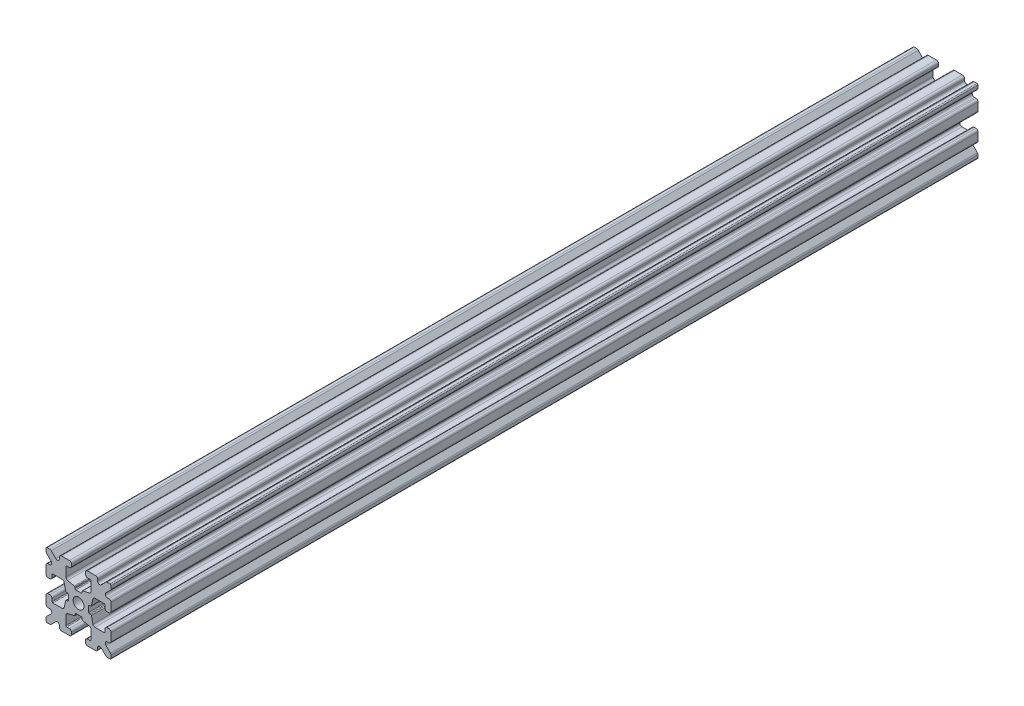
SolidWorks part; units mm, degrees
ref_plane "Front Plane" through (0, 0, 0) normal (0, 0, 1) x (1, 0, 0)
ref_plane "Top Plane" through (0, 0, 0) normal (0, 1, 0) x (1, 0, 0)
ref_plane "Right Plane" through (0, 0, 0) normal (1, 0, 0) x (0, 0, -1)
sketch "Sketch1" plane through (0, 0, 0) normal (0, 0, 1) x (1, 0, 0)
  line L1 (-7.5, -7.5) -> (7.5, -7.5)
  line L2 (-7.5, -7.5) -> (-7.5, 7.5)
  line L3 (-7.5, 7.5) -> (7.5, 7.5)
  line L4 (7.5, -7.5) -> (7.5, 7.5)
  line L5 (-7.5, -7.5) -> (7.5, 7.5) construction
  line L6 (-7.5, 7.5) -> (7.5, -7.5) construction
  circle A0 centre (0, 0) radius 1.25
  point P0 (0, 0)
  dimension "D2" = 2.5
  dimension "D1" = 15
extrude "Boss-Extrude1" add sketch "Sketch1" along normal mid plane 200
fillet "Fillet1" radius 0.25 4 edges at (7.5, -7.5, 0) (-7.5, -7.5, 0) (7.5, 7.5, 0) (-7.5, 7.5, 0)
sketch "Sketch2" plane through (0, 0, 100) normal (0, 0, 1) x (1, 0, 0)
  line L0 (-7.5, 7.25) -> (-7.5, -7.25) construction
  line L1 (-7.5, 1.6) -> (-6.1, 1.6)
  line L2 (-7.5, 1.6) -> (-7.5, -1.6)
  line L3 (-7.5, -1.6) -> (-6.1, -1.6)
  line L4 (-6.1, 1.6) -> (-6.1, 2.9)
  line L5 (0, 0) -> (-12.1036, 0) construction
  line L6 (-6.1, -2.9) -> (-3.4, -2.9)
  line L7 (0, 0) -> (-7.25, 7.25) construction
  line L8 (-6.1, 2.9) -> (-3.4, 2.9)
  line L9 (-3.4, -2.9) -> (-3.4, 2.9)
  line L10 (55, 0) -> (-55, 0) construction
  line L11 (-6.1, -2.9) -> (-6.1, -1.6)
  line L12 (2.9, 6.1) -> (1.6, 6.1)
  line L13 (2.9, 3.4) -> (-2.9, 3.4)
  line L14 (-2.9, 6.1) -> (-2.9, 3.4)
  line L15 (2.9, 6.1) -> (2.9, 3.4)
  line L16 (-1.6, 6.1) -> (-2.9, 6.1)
  line L17 (1.6, 7.5) -> (1.6, 6.1)
  line L18 (-1.6, 7.5) -> (1.6, 7.5)
  line L19 (-1.6, 7.5) -> (-1.6, 6.1)
  line L20 (-1.6, -7.5) -> (-1.6, -6.1)
  line L21 (-1.6, -7.5) -> (1.6, -7.5)
  line L22 (1.6, -7.5) -> (1.6, -6.1)
  line L23 (-1.6, -6.1) -> (-2.9, -6.1)
  line L24 (2.9, -6.1) -> (2.9, -3.4)
  line L25 (-2.9, -6.1) -> (-2.9, -3.4)
  line L26 (2.9, -3.4) -> (-2.9, -3.4)
  line L27 (2.9, -6.1) -> (1.6, -6.1)
  line L28 (6.1, -2.9) -> (6.1, -1.6)
  line L29 (3.4, -2.9) -> (3.4, 2.9)
  line L30 (6.1, 2.9) -> (3.4, 2.9)
  line L31 (6.1, -2.9) -> (3.4, -2.9)
  line L32 (6.1, 1.6) -> (6.1, 2.9)
  line L33 (7.5, -1.6) -> (6.1, -1.6)
  line L34 (7.5, 1.6) -> (7.5, -1.6)
  line L35 (7.5, 1.6) -> (6.1, 1.6)
  dimension "D1" = 3.2
  dimension "D2" = 5.8
  dimension "D3" = 1.4
  dimension "D4" = 2.7
extrude "Cut-Extrude1" cut sketch "Sketch2" against normal through all
sketch "Sketch4" plane through (0, 0, 100) normal (0, 0, 1) x (1, 0, 0)
  line L0 (-3.4, 2.9) -> (-2.75, 0)
  line L1 (55, 0) -> (-55, 0) construction
  line L2 (-2.75, 0) -> (-3.4, -2.9)
  line L3 (-3.4, -2.9) -> (-3.4, 2.9) construction
  line L4 (-3.4, 2.9) -> (-3.4, -2.9)
  line L5 (-2.9, 3.4) -> (0, 2.75)
  line L6 (0, 2.75) -> (2.9, 3.4)
  line L7 (2.9, 3.4) -> (-2.9, 3.4)
  line L8 (3.4, 2.9) -> (2.75, 0)
  line L9 (2.75, 0) -> (3.4, -2.9)
  line L10 (3.4, -2.9) -> (3.4, 2.9)
  line L11 (-2.9, -3.4) -> (0, -2.75)
  line L12 (0, -2.75) -> (2.9, -3.4)
  line L13 (2.9, -3.4) -> (-2.9, -3.4)
  circle A2 centre (0, 0) radius 2.75
  circle A3 centre (0, 0) radius 2.75 construction
  dimension "D1" = 1.5
extrude "Cut-Extrude3" cut sketch "Sketch4" against normal through all
fillet "Fillet3" radius 0.5 16 edges at (-6.1, -1.6, 0) (-7.5, -1.6, 0) (-6.1, 1.6, 0) (-7.5, 1.6, 0) (-1.6, -7.5, 0) (-1.6, -6.1, 0) (1.6, -7.5, 0) (1.6, -6.1, 0) (6.1, -1.6, 0) (7.5, -1.6, 0) (7.5, 1.6, 0) (6.1, 1.6, 0) (1.6, 7.5, 0) (1.6, 6.1, 0) (-1.6, 7.5, 0) (-1.6, 6.1, 0)
fillet "Fillet4" radius 0.5 8 edges at (-3.4, 2.9, 0) (-3.4, -2.9, 0) (2.9, -3.4, 0) (-2.9, -3.4, 0) (3.4, -2.9, 0) (3.4, 2.9, 0) (-2.9, 3.4, 0) (2.9, 3.4, 0)
fillet "Fillet5" radius 3 4 edges at (0, -2.75, 0) (2.75, 0, 0) (-2.75, 0, 0) (0, 2.75, 0)
fillet "Fillet6" radius 0.2 8 edges at (-2.9, -6.1, 0) (2.9, -6.1, 0) (6.1, -2.9, 0) (6.1, 2.9, 0) (2.9, 6.1, 0) (-2.9, 6.1, 0) (-6.1, -2.9, 0) (-6.1, 2.9, 0)
sketch "Sketch5" plane through (0, 0, 100) normal (0, 0, 1) x (1, 0, 0)
  line L0 (0, 0) -> (-7.25, 7.25) construction
  line L1 (-7.5, 6.4393) -> (-5.4607, 4.4)
  line L2 (-6.4393, 7.5) -> (-4.4, 5.4607)
  line L3 (-7.5, 4.4) -> (-5.4607, 4.4)
  line L4 (-3.8003, 2.9) -> (-5.9, 2.9) construction
  line L5 (0, 0) -> (-12.1819, 0) construction
  line L6 (-4.4, 7.5) -> (-4.4, 5.4607)
  line L7 (-2.9, 5.9) -> (-2.9, 3.8003) construction
  line L8 (-7.5, 6.4393) -> (-7.5, 4.4)
  line L9 (-7.5, 7.25) -> (-7.5, 2.1) construction
  line L10 (2.1, -7.5) -> (7.25, -7.5) construction
  line L11 (7.5, -7.25) -> (7.5, -2.1) construction
  line L12 (7.25, 7.5) -> (2.1, 7.5) construction
  line L13 (-2.1, 7.5) -> (-7.25, 7.5) construction
  line L14 (-4.4, 7.5) -> (-6.4393, 7.5)
  line L16 (55, 0) -> (-55, 0) construction
  line L17 (0, 0) -> (0, 10.993) construction
  line L18 (0, -54.6431) -> (0, 54.6431) construction
  line L20 (4.4, 7.5) -> (6.4393, 7.5)
  line L22 (7.5, 6.4393) -> (7.5, 4.4)
  line L23 (4.4, 7.5) -> (4.4, 5.4607)
  line L24 (7.5, 4.4) -> (5.4607, 4.4)
  line L25 (6.4393, 7.5) -> (4.4, 5.4607)
  line L26 (7.5, 6.4393) -> (5.4607, 4.4)
  line L27 (7.5, -6.4393) -> (5.4607, -4.4)
  line L28 (6.4393, -7.5) -> (4.4, -5.4607)
  line L29 (7.5, -4.4) -> (5.4607, -4.4)
  line L30 (4.4, -7.5) -> (4.4, -5.4607)
  line L31 (7.5, -6.4393) -> (7.5, -4.4)
  line L33 (4.4, -7.5) -> (6.4393, -7.5)
  line L36 (-4.4, -7.5) -> (-6.4393, -7.5)
  line L38 (-7.5, -6.4393) -> (-7.5, -4.4)
  line L39 (-4.4, -7.5) -> (-4.4, -5.4607)
  line L40 (-7.5, -4.4) -> (-5.4607, -4.4)
  line L41 (-6.4393, -7.5) -> (-4.4, -5.4607)
  line L42 (-7.5, -6.4393) -> (-5.4607, -4.4)
  dimension "D1" = 1.5
  dimension "D2" = 1.5
  dimension "D3" = 1.5
extrude "Cut-Extrude4" cut sketch "Sketch5" against normal through all
fillet "Fillet8" radius 0.5 24 edges at (-5.4607, 4.4, 0) (-7.5, 4.4, 0) (-5.4607, -4.4, 0) (-7.5, -4.4, 0) (-4.4, -7.5, 0) (-4.4, -5.4607, 0) (4.4, -7.5, 0) (4.4, -5.4607, 0) (5.4607, -4.4, 0) (7.5, -4.4, 0) (7.5, 4.4, 0) (5.4607, 4.4, 0) (4.4, 5.4607, 0) (4.4, 7.5, 0) (-4.4, 5.4607, 0) (-4.4, 7.5, 0) (-6.4393, 7.5, 0) (-7.5, 6.4393, 0) (6.4393, 7.5, 0) (7.5, 6.4393, 0) (6.4393, -7.5, 0) (7.5, -6.4393, 0) (-6.4393, -7.5, 0) (-7.5, -6.4393, 0)
sketch "Sketch6" plane through (0, 0, 100) normal (0, 0, 1) x (1, 0, 0)
  line L0 (0, 0) -> (0, 11.013) construction
  line L1 (0.6561, 2.8971) -> (2.1235, 2.8971) construction
  line L2 (0, -54.6431) -> (0, 54.6431) construction
  line L3 (0, 0) -> (7.25, 7.25) construction
  line L4 (7.5, 0.8255) -> (7.5, -0.8255)
  line L5 (2.3471, 0.8255) -> (7.5, 0.8255)
  line L6 (0, 0) -> (12.4016, 0) construction
  line L7 (0.8255, -7.5) -> (-0.8255, -7.5)
  line L8 (2.3471, -0.8255) -> (2.3471, 0.8255)
  line L9 (0.8255, -2.3471) -> (0.8255, -7.5)
  line L10 (7.5, -0.8255) -> (2.3471, -0.8255)
  line L11 (-7.5, -0.8255) -> (-2.3471, -0.8255)
  line L12 (-2.3471, -0.8255) -> (-2.3471, 0.8255)
  line L13 (-0.8255, -2.3471) -> (0.8255, -2.3471)
  line L14 (-0.8255, 7.5) -> (-0.8255, 2.3471)
  line L15 (-0.8255, 2.3471) -> (0.8255, 2.3471)
  line L16 (-0.8255, -7.5) -> (-0.8255, -2.3471)
  line L17 (0.8255, 2.3471) -> (0.8255, 7.5)
  line L18 (0.8255, 7.5) -> (-0.8255, 7.5)
  line L19 (3.9, 7.5) -> (2.1, 7.5) construction
  line L20 (-2.3471, 0.8255) -> (-7.5, 0.8255)
  line L21 (-7.5, 0.8255) -> (-7.5, -0.8255)
  point P5 (0, -2.5973)
  point P7 (0, 2.5973)
  dimension "D3" = 0.55
  dimension "D1" = 1.651
extrude "Cut-Extrude5" cut sketch "Sketch6" against normal through all
fillet "Fillet10" radius 0.2 16 edges at (-2.935, 0.8255, 0) (-2.935, -0.8255, 0) (2.935, -0.8255, 0) (2.935, 0.8255, 0) (0.8255, 2.935, 0) (-0.8255, 2.935, 0) (-2.3471, 0.8255, 0) (-2.3471, -0.8255, 0) (0.8255, 2.3471, 0) (-0.8255, 2.3471, 0) (2.3471, 0.8255, 0) (2.3471, -0.8255, 0) (0.8255, -2.935, 0) (0.8255, -2.3471, 0) (-0.8255, -2.3471, 0) (-0.8255, -2.935, 0)
